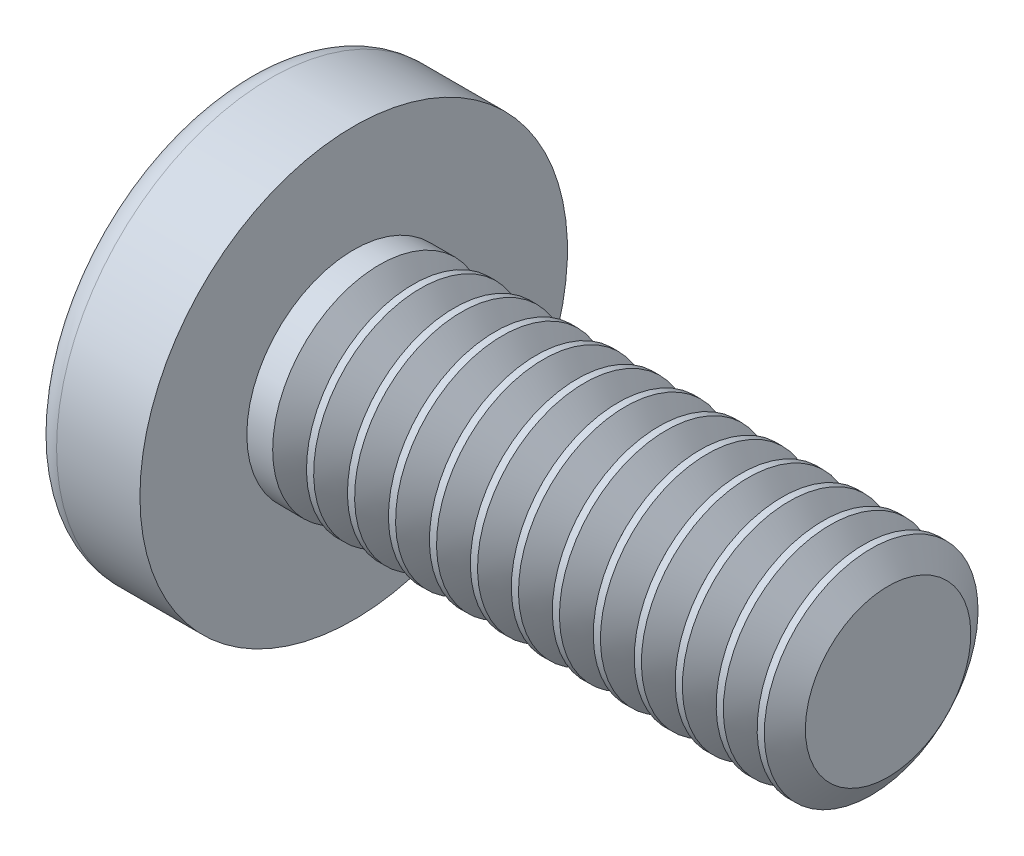
SolidWorks part; units mm, degrees
ref_plane "Plane1" through (0, 0, 0) normal (0, 0, 1) x (1, 0, 0)
ref_plane "Plane2" through (0, 0, 0) normal (0, 1, 0) x (1, 0, 0)
ref_plane "Plane3" through (0, 0, 0) normal (1, 0, 0) x (0, 0, -1)
sketch "BodySke" plane through (0, 0, 0) normal (0, 0, 1) x (1, 0, 0)
  line L0 (1.6, 1) -> (1.6, 2)
  line L1 (2, 6.35) -> (2, -3.175) construction
  line L2 (-25.4, 0) -> (127, 0) construction
  line L3 (6.6, 0) -> (0, 0)
  line L4 (1.6, 1) -> (6.6, 1)
  line L5 (6.6, 1) -> (6.6, 0)
  line L6 (0.8201, 2) -> (1.6, 2)
  line L7 (1.6, -1) -> (6.6, -1) construction
  line L8 (1.6, 6.35) -> (1.6, -3.175) construction
  arc A0 (0.6271, 1.9027) -> (0, 0) centre (3.2, 0) ccw
  arc A2 (0.6271, 1.9027) -> (0.8201, 2) centre (0.8201, 1.76) cw
  dimension "Head_fillet_rad" = 0.24
  dimension "Head_crown_rad" = 3.2
  dimension "Head_ht" = 1.6
  dimension "Diameter" = 2
  dimension "Length" = 5
  dimension "Head_dia" = 4
  dimension "Advance" = 0.4
  dimension "Thread_nom" = 5
revolve "Base-Revolve" add sketch "BodySke" angle 360 about L2
cosmetic thread "ThreadCosmetic" [suppressed] parameters "Thread_length"=4.6, "Thread_minor"=1.548
sketch "Sketch3" plane through (0, 0, 0) normal (1, 0, 0) x (0, 0, -1)
  line L0 (0.24, -0.91) -> (-0.24, -0.91)
  line L1 (0.24, -0.91) -> (0.24, 0.91)
  line L2 (-0.24, 0.91) -> (0.24, 0.91)
  line L3 (-0.24, 0.91) -> (-0.24, -0.91)
  dimension "D1" = 0.91
  dimension "Cross_dia" = 1.82
  dimension "D2" = 0.24
  dimension "Cross_width" = 0.48
ref_plane "Plane4" through (1.19, 0, 0) normal (1, 0, 0) x (0, 0, -1)
sketch "Sketch4" plane through (1.19, 0, 0) normal (1, 0, 0) x (0, 0, -1)
  line L0 (0.12, -0.12) -> (-0.12, -0.12)
  line L1 (0.12, -0.12) -> (0.12, 0.12)
  line L2 (-0.12, 0.12) -> (0.12, 0.12)
  line L3 (-0.12, 0.12) -> (-0.12, -0.12)
  dimension "D1" = 0.24
  dimension "D2" = 0.24
  dimension "D3" = 0.12
  dimension "D4" = 0.12
loft "Cut-Loft1" cut profiles "Sketch3", "Sketch4"
pattern_circular "CirPattern1" count 2 every 90 about axis through (0, 0, 0) along (1, 0, 0) of "Cut-Loft1"
sketch "ThdSchSke" plane through (0, 0, 0) normal (0, 0, 1) x (1, 0, 0)
  line L0 (2, -0.774) -> (1.8418, -1)
  line L1 (2, -0.774) -> (2.1582, -1)
  line L2 (2.1582, -1) -> (2.1582, -1.25)
  line L3 (-3.175, 0) -> (5.1513, 0) construction
  line L5 (2.1582, -1.25) -> (1.8418, -1.25)
  line L6 (1.8418, -1.25) -> (1.8418, -1)
  dimension "Thread_minor" = 1.548
  dimension "Diameter" = 2
  dimension "Start" = 2
  dimension "SideAngle" = 55
  dimension "VeeAngle" = 70
  dimension "Overcut" = 2.5
revolve "ThreadSchematic" cut sketch "ThdSchSke" angle 360 about L3
pattern_linear "ThdSchPat" count 13 spacing 0.3833 along (1, 0, 0) of "ThreadSchematic"
equation "\"D1@Sketch3\" = \"Cross_dia@Sketch3\" / 2"
equation "\"D2@Sketch3\" = \"Cross_width@Sketch3\" / 2"
equation "\"D1@Sketch4\" = \"Cross_width@Sketch3\" *.5"
equation "\"D2@Sketch4\" = \"D1@Sketch4\""
equation "\"D3@Sketch4\" = \"D1@Sketch4\" / 2"
equation "\"D4@Sketch4\" = \"D2@Sketch4\" / 2"
equation "\"Thread_length@ThreadCosmetic\" = ((sgn( (\"Length@BodySke\" - \"Advance@BodySke\" ) - \"Thread_nom@BodySke\" )-1)*( (\"Length@BodySke\" - \"Advance@BodySke\" ) - \"Thread_nom@BodySke\" ))/-2+ \"Thread_nom@BodySke\""
equation "\"Thread_minor@ThdSchSke\" = \"Thread_minor@ThreadCosmetic\""
equation "\"Diameter@ThdSchSke\" = \"Diameter@BodySke\""
equation "\"Overcut@ThdSchSke\" = \"Diameter@BodySke\" * 1.25"
equation "\"Start@ThdSchSke\" = \"Head_ht@BodySke\" + \"Length@BodySke\" - \"Thread_length@ThreadCosmetic\"  '---Non-countersunk---"
equation "\"Num_threads@ThdSchPat\" = int( \"Thread_length@ThreadCosmetic\" / \"Advance@BodySke\" + 0.999 )  + 1"
equation "\"Advance@ThdSchPat\" = \"Thread_length@ThreadCosmetic\" /  (\"Num_threads@ThdSchPat\" - 1) 'relax it"
